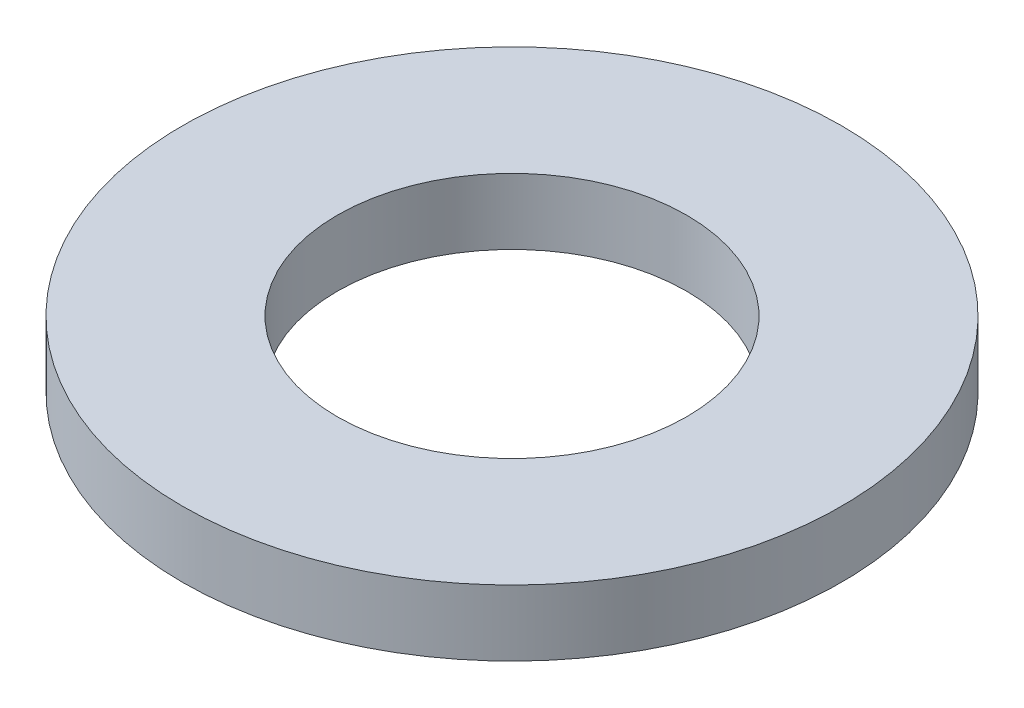
SolidWorks part; units mm, degrees
ref_plane "Front" through (0, 0, 0) normal (0, 0, 1) x (1, 0, 0)
ref_plane "Top" through (0, 0, 0) normal (0, 1, 0) x (1, 0, 0)
ref_plane "Right" through (0, 0, 0) normal (1, 0, 0) x (0, 0, -1)
sketch "Sketch1" plane through (0, 0, 0) normal (0, 1, 0) x (1, 0, 0)
  circle A0 centre (0, 0) radius 2.65
  circle A1 centre (0, 0) radius 5
extrude "Extrude1" add sketch "Sketch1" along normal blind 1
